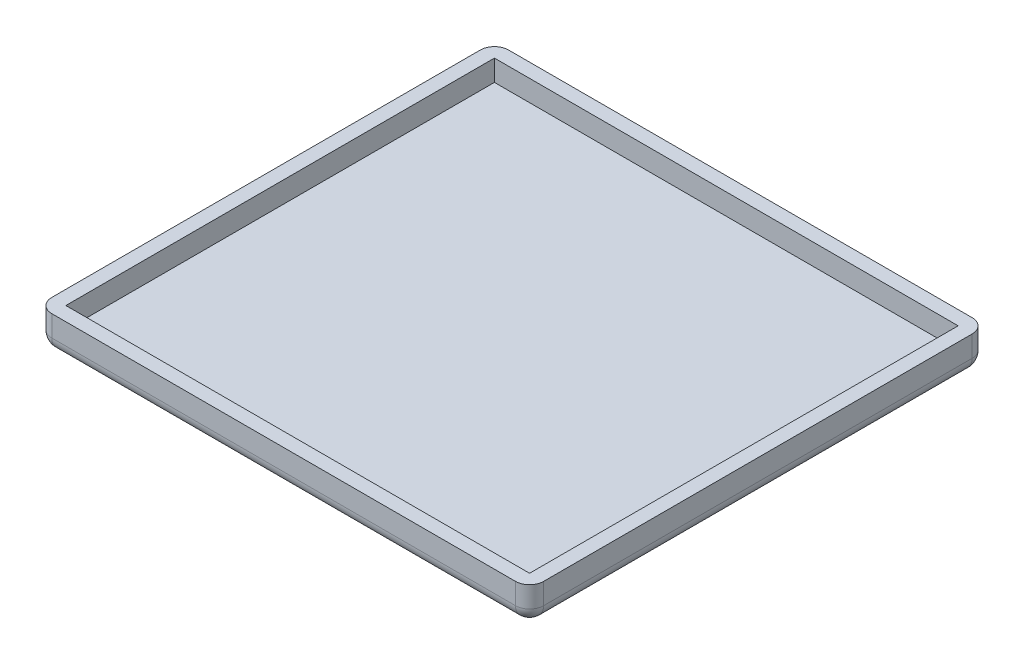
SolidWorks part; units mm, degrees
ref_plane "Front Plane" through (0, 0, 0) normal (0, 0, 1) x (1, 0, 0)
ref_plane "Top Plane" through (0, 0, 0) normal (0, 1, 0) x (1, 0, 0)
ref_plane "Right Plane" through (0, 0, 0) normal (1, 0, 0) x (0, 0, -1)
sketch "Sketch1" plane through (0, 0, 0) normal (0, 1, 0) x (1, 0, 0)
  line L0 (-33, -30.5) -> (33, -30.5)
  line L1 (-35, 32.5) -> (35, 32.5)
  line L2 (-35, 32.5) -> (-35, -32.5)
  line L3 (-35, -32.5) -> (35, -32.5)
  line L4 (35, 32.5) -> (35, -32.5)
  line L5 (-35, 32.5) -> (35, -32.5) construction
  line L6 (-35, -32.5) -> (35, 32.5) construction
  line L7 (33, 30.5) -> (33, -30.5)
  line L8 (-33, 30.5) -> (33, 30.5)
  line L9 (-33, 30.5) -> (-33, -30.5)
  point P0 (0, 0)
  dimension "D1" = 2
extrude "Boss-Extrude1" add sketch "Sketch1" along normal blind 5
sketch "Sketch2" plane through (0, 0, 0) normal (0, 1, 0) x (1, 0, 0)
  line L0 (-33, 30.5) -> (33, 30.5)
  line L1 (33, 30.5) -> (33, -30.5)
  line L2 (33, -30.5) -> (-33, -30.5)
  line L3 (-33, -30.5) -> (-33, 30.5)
extrude "Boss-Extrude2" add sketch "Sketch2" along normal blind 2
fillet "Fillet2" radius 2 8 edges at (0, 0, -32.5) (-35, 2.5, -32.5) (35, 0, 0) (35, 2.5, -32.5) (35, 2.5, 32.5) (0, 0, 32.5) (-35, 2.5, 32.5) (-35, 0, 0)
